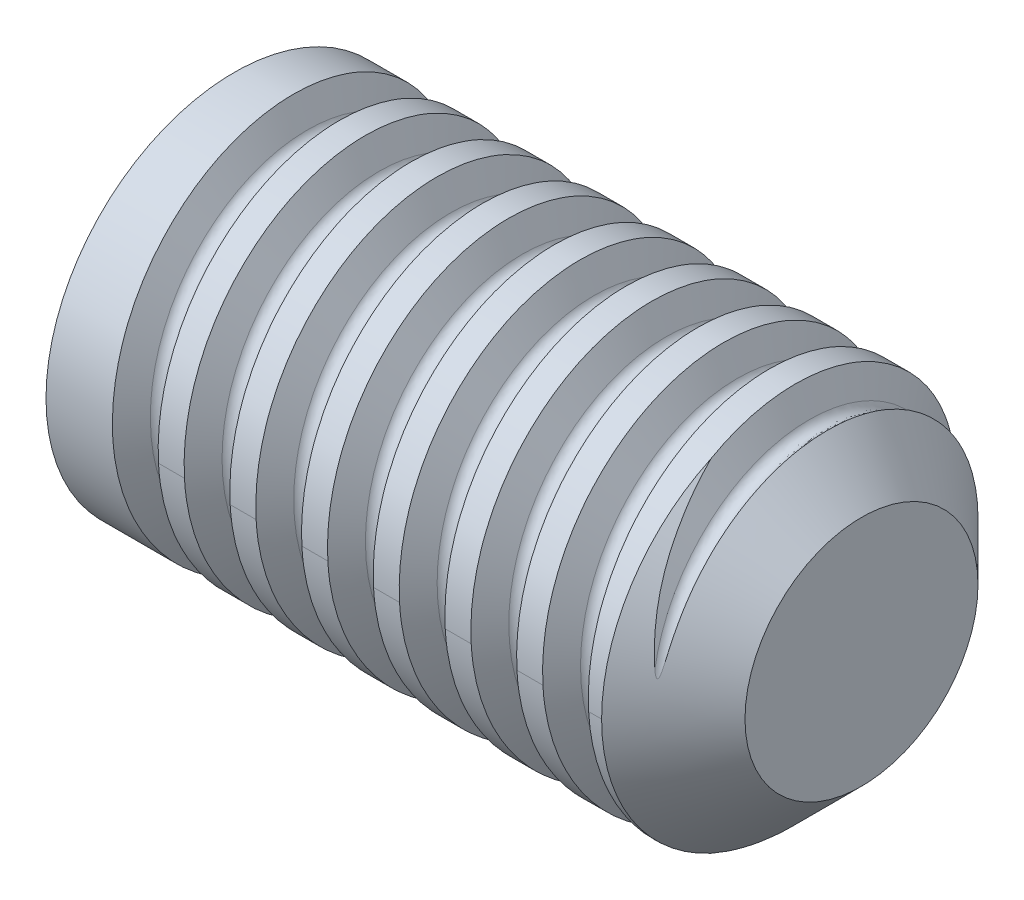
SolidWorks part; units mm, degrees
material "AISI Type 316L stainless steel"
ref_plane "Front Plane" through (0, 0, 0) normal (0, 0, 1) x (1, 0, 0)
ref_plane "Top Plane" through (0, 0, 0) normal (0, 1, 0) x (1, 0, 0)
ref_plane "Right Plane" through (0, 0, 0) normal (1, 0, 0) x (0, 0, -1)
sketch "Sketch1" plane through (0, 0, 0) normal (0, 0, 1) x (1, 0, 0)
  line L0 (-90.7066, 0) -> (94.9801, 0) construction
  line L1 (4, 0) -> (4, 2.1)
  line L4 (11, 0) -> (11, 2.1)
  line L5 (11, 2.1) -> (4, 2.1)
  line L7 (4, 0) -> (11, 0)
  point P5 (0, 2.4878)
  point P9 (0, 2.6342)
  dimension "D1" = 7
  dimension "D2" = 4
  dimension "D3" = 2.1
revolve "Revolve1" add sketch "Sketch1" angle 360 about L0
chamfer "Chamfer1" distance 0.8 angle 45 1 edges at (11, 0, 2.1)
sketch "Sketch3" plane through (0, 0, 0) normal (1, 0, 0) x (0, 0, -1)
  line L1 (-1.7321, 0) -> (-0.866, -1.5)
  line L2 (-0.866, -1.5) -> (0.866, -1.5)
  line L3 (0.866, -1.5) -> (1.7321, 0)
  line L4 (1.7321, 0) -> (0.866, 1.5)
  line L5 (0.866, 1.5) -> (-0.866, 1.5)
  line L6 (-0.866, 1.5) -> (-1.7321, 0)
  circle A0 centre (0, 0) radius 1.5 construction
  dimension "D1" = 3
extrude "Cut-Extrude1" cut sketch "Sketch3" along normal blind 7.5
sketch "Sketch5" plane through (11, 0, 0) normal (1, 0, 0) x (0, 0, -1)
  circle A0 centre (0, 0) radius 2.1
  dimension "D1" = 4.2
curve "Helix/Spiral1" pitch 0.8 height 6.5 turns 8.125
sketch "Sketch8" plane through (0, 0, 0) normal (0, 1, 0) x (1, 0, 0)
  line L0 (11, 2.2645) -> (11, 1.6581) construction
  line L1 (11.1, 1.8314) -> (11.5251, 2.5677)
  line L2 (11.5251, 2.5677) -> (10.4749, 2.5677)
  line L3 (10.4749, 2.5677) -> (10.9, 1.8314)
  line L4 (11, -1.3) -> (11, 1.3) construction
  circle A0 centre (11, 2.2645) radius 0.3032 construction
  arc A1 (11.1, 1.8314) -> (10.9, 1.8314) centre (11, 1.8891) cw
  point P10 (11, 2.488)
  point P11 (11, 2.3638)
  point P12 (0, 0)
  point P14 (11, 2.1185)
  point P15 (11, 2.158)
  point P16 (11, 2.2173)
  point P17 (11, 2.2645)
  dimension "D2" = 0.1155
  dimension "D1" = 0.6064
sweep "Cut-Sweep1" cut profiles "Sketch8" path "Helix/Spiral1"
